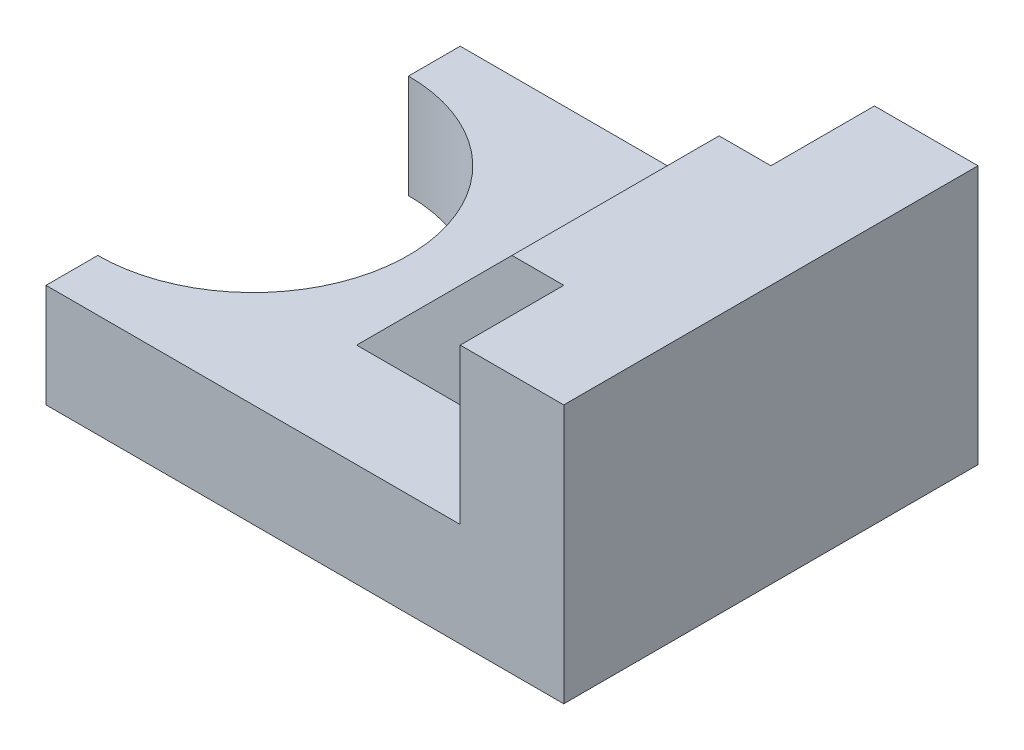
SolidWorks part; units mm, degrees
ref_plane "Front Plane" through (0, 0, 0) normal (0, 0, 1) x (1, 0, 0)
ref_plane "Top Plane" through (0, 0, 0) normal (0, 1, 0) x (1, 0, 0)
ref_plane "Right Plane" through (0, 0, 0) normal (1, 0, 0) x (0, 0, -1)
sketch "Sketch1" plane through (0, 0, 0) normal (0, 0, 1) x (1, 0, 0)
  line L0 (25.4882, 8.1356) -> (25.4882, -16.8644)
  line L1 (25.4882, -16.8644) -> (-24.5118, -16.8644)
  line L2 (-24.5118, -16.8644) -> (-24.5118, -6.8644)
  line L3 (-24.5118, -6.8644) -> (-4.5118, -6.8644)
  line L4 (15.4882, -6.8644) -> (15.4882, 8.1356)
  line L5 (15.4882, 8.1356) -> (25.4882, 8.1356)
  line L6 (15.4882, 8.1356) -> (10.4882, 8.1356)
  line L7 (10.4882, 8.1356) -> (-4.5118, -6.8644)
  line L8 (-4.5118, -6.8644) -> (15.4882, -6.8644)
  dimension "D1" = 25
  dimension "D2" = 50
  dimension "D3" = 10
  dimension "D4" = 20
  dimension "D5" = 5
  dimension "D6" = 10
extrude "Boss-Extrude1" add sketch "Sketch1" along normal mid plane 40 contours L8 L3 L2 L1 L0 L5 L4 | L7 L8 L4 L6
sketch "Sketch2" plane through (0, 0, 20) normal (0, 0, 1) x (1, 0, 0)
  line L0 (-4.5118, -6.8644) -> (15.4882, -6.8644)
  line L1 (15.4882, 8.1356) -> (15.4882, -6.8644)
  line L2 (25.4882, 8.1356) -> (25.4882, -16.8644) construction
  line L3 (-4.5118, -6.8644) -> (10.4882, 8.1356)
  line L4 (10.4882, 8.1356) -> (15.4882, 8.1356)
  dimension "D1" = 10
extrude "Cut-Extrude1" cut sketch "Sketch2" against normal blind 10 and the other way through all
sketch "Sketch3" plane through (0, 0, -20) normal (0, 0, -1) x (-1, 0, 0)
  line L0 (4.5118, -6.8644) -> (-15.4882, -6.8644)
  line L1 (-15.4882, 8.1356) -> (-15.4882, -6.8644)
  line L2 (-25.4882, 8.1356) -> (-25.4882, -16.8644) construction
  line L3 (-10.4882, 8.1356) -> (4.5118, -6.8644)
  line L4 (-10.4882, 8.1356) -> (-15.4882, 8.1356)
  dimension "D1" = 10
extrude "Cut-Extrude2" cut sketch "Sketch3" against normal blind 10
sketch "Sketch4" plane through (0, -6.8644, 0) normal (0, 1, 0) x (1, 0, 0)
  line L0 (-24.5118, -20) -> (-24.5118, 20) construction
  line L1 (-24.5118, 15) -> (-24.5118, -15)
  arc A0 (-24.5118, 15) -> (-24.5118, -15) centre (-24.5118, 0) cw
extrude "Cut-Extrude3" cut sketch "Sketch4" against normal up to next
